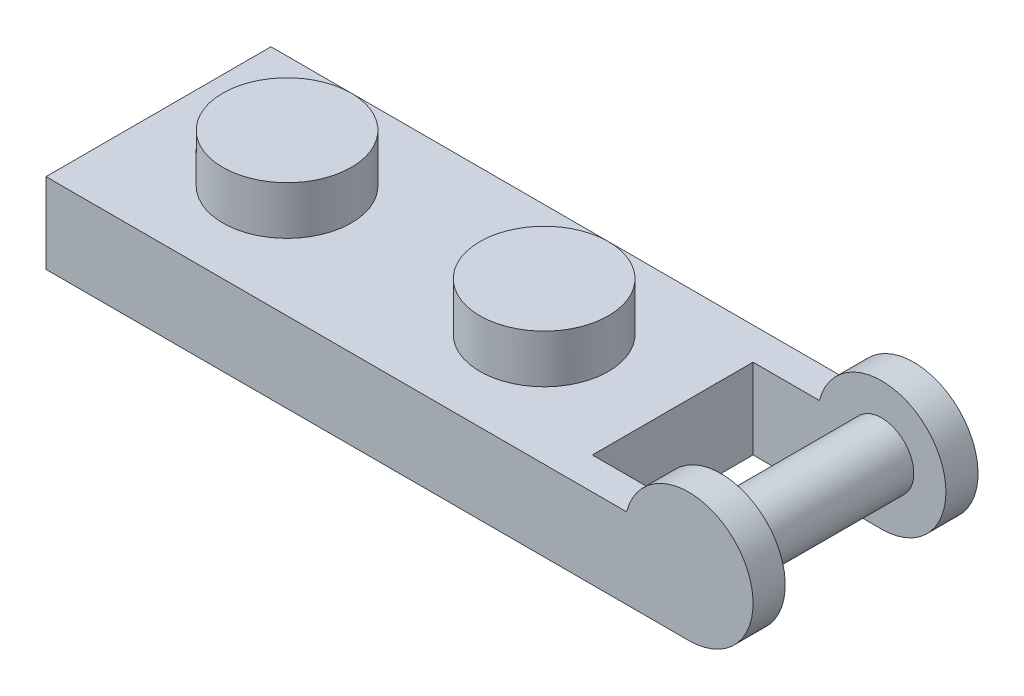
SolidWorks part; units mm, degrees
material "ABS"
ref_plane "Front Plane" through (0, 0, 0) normal (0, 0, 1) x (1, 0, 0)
ref_plane "Top Plane" through (0, 0, 0) normal (0, 1, 0) x (1, 0, 0)
ref_plane "Right Plane" through (0, 0, 0) normal (1, 0, 0) x (0, 0, -1)
sketch "Sketch1" plane through (0, 0, 0) normal (0, 0, 1) x (1, 0, 0)
  line L0 (-10.16, 0) -> (10.16, 0)
  line L1 (10.16, 0) -> (10.16, -3.175)
  line L2 (10.16, -3.175) -> (-10.16, -3.175)
  line L3 (-10.16, -3.175) -> (-10.16, 0)
  point P4 (0, -3.175)
  dimension "D1" = 20.32
  dimension "D2" = 3.175
extrude "Boss-Extrude2" add sketch "Sketch1" along normal mid plane 8.89
sketch "Sketch3" plane through (0, 0, 0) normal (0, 1, 0) x (1, 0, 0)
  line L0 (-10.16, 4.445) -> (0, -4.445) construction
  line L1 (10.16, -4.445) -> (-10.16, -4.445) construction
  line L2 (0, -4.445) -> (10.16, 4.445) construction
  circle A0 centre (-5.08, 0) radius 2.54
  circle A1 centre (5.08, 0) radius 2.54
  dimension "D1" = 5.08
  dimension "D2" = 5.08
extrude "Boss-Extrude3" add sketch "Sketch3" along normal blind 1.905
sketch "Sketch4" plane through (0, -3.175, 0) normal (0, -1, 0) x (1, 0, 0)
  line L0 (-8.89, 2.54) -> (-8.89, -2.54)
  line L1 (-8.89, -2.54) -> (8.89, -2.54)
  line L2 (8.89, -2.54) -> (8.89, 2.54)
  line L3 (8.89, 2.54) -> (-8.89, 2.54)
  line L5 (-10.16, 4.445) -> (-10.16, -4.445) construction
  line L6 (10.16, 4.445) -> (10.16, -4.445) construction
  line L7 (-10.16, -4.445) -> (0, 4.445) construction
  line L8 (-10.16, -4.445) -> (10.16, -4.445) construction
  line L9 (-10.16, 4.445) -> (10.16, 4.445) construction
  line L10 (0, 4.445) -> (10.16, -4.445) construction
  point P2 (-8.89, 0)
  dimension "D1" = 5.08
  dimension "D2" = 1.27
  dimension "D3" = 1.27
extrude "Cut-Extrude1" cut sketch "Sketch4" against normal blind 1.905
sketch "Sketch5" plane through (0, -1.27, 0) normal (0, -1, 0) x (1, 0, 0)
  line L0 (-10.16, -4.445) -> (0, 4.445) construction
  line L1 (-10.16, 4.445) -> (10.16, 4.445) construction
  line L2 (0, 4.445) -> (10.16, -4.445) construction
  circle A0 centre (-5.08, 0) radius 1.905
  circle A1 centre (5.08, 0) radius 1.905
  dimension "D1" = 3.81
  dimension "D2" = 3.81
extrude "Cut-Extrude2" cut sketch "Sketch5" against normal blind 2.54
sketch "Sketch6" plane through (0, -1.27, 0) normal (0, -1, 0) x (1, 0, 0)
  circle A0 centre (0, 0) radius 1.905
  circle A1 centre (0, 0) radius 0.9525
  dimension "D1" = 3.81
  dimension "D2" = 1.905
extrude "Boss-Extrude4" add sketch "Sketch6" along normal up to surface (1.905 mm away) up to face at (0, -3.175, 0)
sketch "Sketch8" plane through (0, 0, 4.445) normal (0, 0, 1) x (1, 0, 0)
  line L0 (10.16, -3.175) -> (15.24, -3.175)
  line L1 (17.78, -0.635) -> (19.7248, -0.635) construction
  line L2 (10.16, -3.175) -> (10.16, 0) construction
  line L3 (10.16, 0) -> (12.7807, 0)
  line L4 (10.16, -3.175) -> (10.16, 0)
  arc A0 (15.24, -3.175) -> (12.7807, 0) centre (15.24, -0.635) ccw
  dimension "D1" = 5.08
  dimension "D2" = 7.62
extrude "Boss-Extrude5" add sketch "Sketch8" against normal blind 1.27
mirror "Mirror1" about plane through (0, 0, 0) normal (0, 0, 1) of "Boss-Extrude5"
sketch "Sketch9" plane through (0, 0, 0) normal (0, 0, 1) x (1, 0, 0)
  circle A0 centre (15.24, -0.635) radius 1.27
  dimension "D1" = 2.54
extrude "Boss-Extrude6" add sketch "Sketch9" along normal through all and the other way through all
